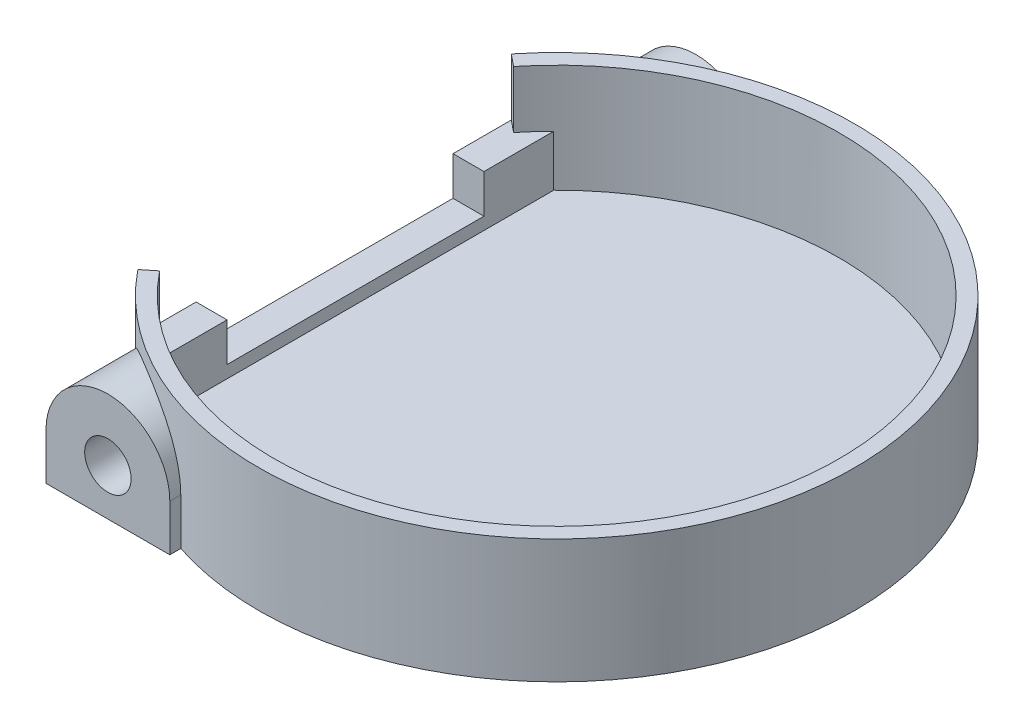
SolidWorks part; units mm, degrees
ref_plane "Front Plane" through (0, 0, 0) normal (0, 0, 1) x (1, 0, 0)
ref_plane "Top Plane" through (0, 0, 0) normal (0, 1, 0) x (1, 0, 0)
ref_plane "Right Plane" through (0, 0, 0) normal (1, 0, 0) x (0, 0, -1)
sketch "Sketch1" plane through (0, 0, 0) normal (0, 1, 0) x (1, 0, 0)
  line L0 (-15, -10.3953) -> (-15, 10.3953)
  line L1 (-16, -10.7034) -> (-16, 10.7034)
  circle A0 centre (0, 0) radius 18 construction
  arc A1 (-15, -10.3953) -> (-15, 10.3953) centre (0, 0) ccw
  circle A2 centre (0, 0) radius 18.25 construction
  arc A3 (-16, -10.7034) -> (-16, 10.7034) centre (0, 0) ccw
  dimension "D1" = 36
  dimension "D3" = 15
  dimension "D2" = 0.25
  dimension "D4" = 1
extrude "Boss-Extrude1" add sketch "Sketch1" along normal blind 7
sketch "Sketch2" plane through (0, 0, 0) normal (0, -1, 0) x (1, 0, 0)
  line L1 (-16, 10.7034) -> (-16, -10.7034)
  line L2 (-16, 10.7034) -> (-16, -10.7034)
  arc A1 (-16, -10.7034) -> (-16, 10.7034) centre (0, 0) ccw
  arc A2 (-16, -10.7034) -> (-16, 10.7034) centre (0, 0) ccw
  dimension "D1" = 0
extrude "Boss-Extrude2" add sketch "Sketch2" along normal blind 1
sketch "Sketch3" plane through (0, 7, 0) normal (0, 1, 0) x (1, 0, 0)
  line L1 (-21.664, 16.3886) -> (-15, 16.3886)
  line L2 (-21.664, 16.3886) -> (-21.664, -17.347)
  line L3 (-21.664, -17.347) -> (-15, -17.347)
  line L4 (-15, 16.3886) -> (-15, -17.347)
extrude "Cut-Extrude1" cut sketch "Sketch3" against normal through all
sketch "Sketch4" plane through (0, 0, 0) normal (0, 1, 0) x (1, 0, 0)
  line L0 (-15, 12.0649) -> (-15, -12.0649)
  line L1 (-13, -12.8087) -> (-13, 12.8087)
  line L2 (-13, -8) -> (-13, 8) construction
  line L3 (-13, 12.8087) -> (-15, 12.0649)
  line L4 (-15, 0) -> (-2.5, 0) construction
  line L5 (-13, -12.8087) -> (-15, -12.0649)
  arc A0 (-15, -10.3953) -> (-15, 10.3953) centre (0, 0) ccw construction
  point P16 (-13, 0)
extrude "Boss-Extrude3" add sketch "Sketch4" along normal blind 3.3
sketch "Sketch5" plane through (0, 7, 0) normal (0, 1, 0) x (1, 0, 0)
  line L0 (0, 0) -> (-15, -12.0649)
  line L3 (-15, -12.0649) -> (-15, 12.0649)
  line L5 (-15, 12.0649) -> (0, 0)
extrude "Cut-Extrude2" cut sketch "Sketch5" against normal up to vertex (3.7 mm away)
sketch "Sketch6" plane through (0, 3.3, 0) normal (0, 1, 0) x (1, 0, 0)
  line L0 (-15, 12.0649) -> (-15, -12.0649) construction
  line L1 (-17, -8.3) -> (-13, -8.3)
  line L2 (-17, -8.3) -> (-17, 8.3)
  line L3 (-17, 8.3) -> (-13, 8.3)
  line L4 (-13, -8.3) -> (-13, 8.3)
  line L5 (-17, -8.3) -> (-13, 8.3) construction
  line L6 (-17, 8.3) -> (-13, -8.3) construction
  line L7 (-13, -12.8087) -> (-13, 12.8087) construction
  line L8 (-15, 8) -> (-13, 8) construction
  point P0 (-15, 0)
  dimension "D1" = 0.3
extrude "Cut-Extrude3" cut sketch "Sketch6" against normal blind 2.5
ref_plane "Plane1" through (0, 0, 19) normal (0, 0, 1) x (1, 0, 0)
sketch "Sketch7" plane through (0, 0, 19) normal (0, 0, 1) x (1, 0, 0)
  line L0 (-15, 7) -> (-15, 3.3) construction
  line L1 (-14, 2) -> (-14, -1)
  line L2 (-15, -1) -> (19.25, -1) construction
  line L3 (-14, -1) -> (-6, -1)
  line L4 (-6, -1) -> (-6, 2)
  arc A0 (-6, 2) -> (-14, 2) centre (-10, 2) ccw
  circle A1 centre (-10, 2) radius 1.5
  dimension "D1" = 8
  dimension "D2" = 3
  dimension "D3" = 3
  dimension "D4" = 1
extrude "Boss-Extrude4" add sketch "Sketch7" against normal up to surface (1.7283 mm away)
mirror "Mirror1" about plane through (0, 0, 0) normal (0, 0, 1) of "Boss-Extrude4"
